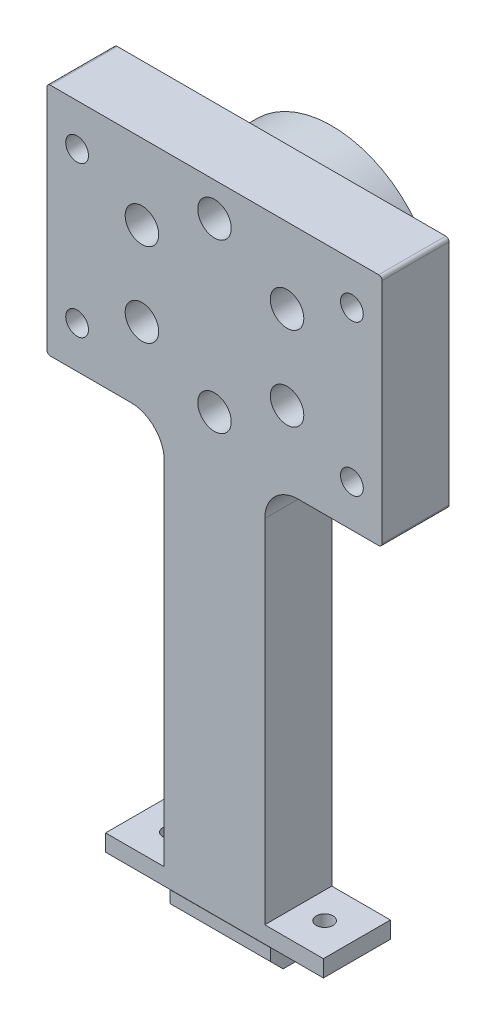
SolidWorks part; units mm, degrees
material "Lega 1060"
ref_plane "Piano frontale" through (0, 0, 0) normal (0, 0, 1) x (1, 0, 0)
ref_plane "Piano superiore" through (0, 0, 0) normal (0, 1, 0) x (1, 0, 0)
ref_plane "Piano destro" through (0, 0, 0) normal (1, 0, 0) x (0, 0, -1)
sketch "Schizzo1" plane through (0, 0, 0) normal (0, 0, 1) x (1, 0, 0)
  arc A6 (-1482, 0) -> (-1488, 0) centre (-1485, 0) ccw
  arc A7 (-1488, 0) -> (-1482, 0) centre (-1485, 0) ccw
  arc A8 (-1475.75, 0) -> (-1444.25, 0) centre (-1460, 0) ccw
  arc A9 (-1444.25, 0) -> (-1475.75, 0) centre (-1460, 0) ccw
extrude "Estrusione-Estrusione2" add sketch "Schizzo1" against normal blind 1
ref_point "Punto1"
sketch "Schizzo2" plane through (0, 0, 0) normal (0, 0, 1) x (1, 0, 0)
  arc A0 (-1479.1506, -12.5) -> (-1484.1506, -12.5) centre (-1481.6506, -12.5) ccw construction
  arc A1 (-1484.1506, -12.5) -> (-1479.1506, -12.5) centre (-1481.6506, -12.5) ccw construction
  arc A2 (-1457.5, -25) -> (-1462.5, -25) centre (-1460, -25) ccw construction
  arc A3 (-1462.5, -25) -> (-1457.5, -25) centre (-1460, -25) ccw construction
  arc A4 (-1435.8494, -12.5) -> (-1440.8494, -12.5) centre (-1438.3494, -12.5) ccw construction
  arc A5 (-1440.8494, -12.5) -> (-1435.8494, -12.5) centre (-1438.3494, -12.5) ccw construction
  arc A6 (-1435.8494, 12.5) -> (-1440.8494, 12.5) centre (-1438.3494, 12.5) ccw construction
  arc A7 (-1440.8494, 12.5) -> (-1435.8494, 12.5) centre (-1438.3494, 12.5) ccw construction
  arc A8 (-1462.5, 25) -> (-1457.5, 25) centre (-1460, 25) ccw construction
  arc A9 (-1457.5, 25) -> (-1462.5, 25) centre (-1460, 25) ccw construction
  arc A10 (-1479.1506, 12.5) -> (-1484.1506, 12.5) centre (-1481.6506, 12.5) ccw construction
  arc A11 (-1484.1506, 12.5) -> (-1479.1506, 12.5) centre (-1481.6506, 12.5) ccw construction
  arc A12 (-1479.1506, -12.5) -> (-1484.1506, -12.5) centre (-1481.6506, -12.5) ccw
  arc A13 (-1484.1506, -12.5) -> (-1479.1506, -12.5) centre (-1481.6506, -12.5) ccw
  arc A14 (-1457.5, -25) -> (-1462.5, -25) centre (-1460, -25) ccw
  arc A15 (-1462.5, -25) -> (-1457.5, -25) centre (-1460, -25) ccw
  arc A16 (-1435.8494, -12.5) -> (-1440.8494, -12.5) centre (-1438.3494, -12.5) ccw
  arc A17 (-1440.8494, -12.5) -> (-1435.8494, -12.5) centre (-1438.3494, -12.5) ccw
  arc A18 (-1435.8494, 12.5) -> (-1440.8494, 12.5) centre (-1438.3494, 12.5) ccw
  arc A19 (-1440.8494, 12.5) -> (-1435.8494, 12.5) centre (-1438.3494, 12.5) ccw
  arc A20 (-1462.5, 25) -> (-1457.5, 25) centre (-1460, 25) ccw
  arc A21 (-1457.5, 25) -> (-1462.5, 25) centre (-1460, 25) ccw
  arc A22 (-1479.1506, 12.5) -> (-1484.1506, 12.5) centre (-1481.6506, 12.5) ccw
  arc A23 (-1484.1506, 12.5) -> (-1479.1506, 12.5) centre (-1481.6506, 12.5) ccw
  arc A24 (-1491.5, 0) -> (-1428.5, 0) centre (-1460, 0) ccw construction
  arc A25 (-1428.5, 0) -> (-1491.5, 0) centre (-1460, 0) ccw construction
  arc A26 (-1491.5, 0) -> (-1428.5, 0) centre (-1460, 0) ccw
  arc A27 (-1428.5, 0) -> (-1491.5, 0) centre (-1460, 0) ccw
extrude "Estrusione-Estrusione3" add sketch "Schizzo2" along normal blind 15
sketch "Schizzo4" plane through (0, 0, 15) normal (0, 0, 1) x (1, 0, 0)
  line L0 (-1460, 0) -> (-1519.7962, 0) construction
  line L5 (-1510, 35) -> (-1410, 35)
  line L6 (-1510, 35) -> (-1510, -35)
  line L7 (-1510, -35) -> (-1410, -35)
  line L8 (-1410, 35) -> (-1410, -35)
  line L9 (-1460, 0) -> (-1460, 38.4815) construction
  circle A0 centre (-1501, 22.5) radius 3.4
  circle A2 centre (-1419, -22.5) radius 3.4
  circle A3 centre (-1419, 22.5) radius 3.4
  circle A16 centre (-1460, 0) radius 31.5 construction
  circle A17 centre (-1501, -22.5) radius 3.4
  dimension "D3" = 35
  dimension "D4" = 50
  dimension "D5" = 9
  dimension "D7" = 6.8
  dimension "D1" = 100
  dimension "D2" = 70
  dimension "D6" = 12.5
extrude "Estrusione-Estrusione4" add sketch "Schizzo4" along normal blind 20
sketch "Schizzo5" plane through (0, 0, -1) normal (0, 0, -1) x (-1, 0, 0)
  circle A0 centre (1438.3494, 12.5) radius 2.5
  circle A1 centre (1438.3494, -12.5) radius 2.5 construction
  circle A2 centre (1460, -25) radius 2.5 construction
  circle A3 centre (1481.6506, -12.5) radius 2.5 construction
  circle A4 centre (1481.6506, 12.5) radius 2.5 construction
  circle A5 centre (1460, 25) radius 2.5 construction
  circle A6 centre (1438.3494, -12.5) radius 2.5
  circle A7 centre (1460, -25) radius 2.5
  circle A8 centre (1481.6506, -12.5) radius 2.5
  circle A9 centre (1481.6506, 12.5) radius 2.5
  circle A10 centre (1460, 25) radius 2.5
extrude "Taglio-Estrusione2" cut sketch "Schizzo5" against normal up to surface (36 mm away) up to face at (-1422.4, -22.5, 35)
sketch "Schizzo6" plane through (0, 0, 35) normal (0, 0, 1) x (1, 0, 0)
  circle A1 centre (-1460, 25) radius 5
  circle A2 centre (-1438.3494, 12.5) radius 5
  circle A3 centre (-1438.3494, -12.5) radius 5
  circle A4 centre (-1460, -25) radius 5
  circle A5 centre (-1481.6506, -12.5) radius 5
  circle A29 centre (-1481.6506, 12.5) radius 5
  circle A30 centre (-1481.6506, 12.5) radius 5
  point P0 (-1460, 0)
  point P13 (-1460, 0)
  dimension "D1" = 2.5
  dimension "D2" = 6
extrude "Taglio-Estrusione3" cut sketch "Schizzo6" against normal blind 10
sketch "Schizzo7" plane through (0, 0, 15) normal (0, 0, -1) x (-1, 0, 0)
  circle A2 centre (1419, 22.5) radius 6
  circle A3 centre (1501, -22.5) radius 6
  circle A4 centre (1501, 22.5) radius 6
  circle A5 centre (1419, -22.5) radius 6
  dimension "D1" = 12
extrude "Taglio-Estrusione4" cut sketch "Schizzo7" against normal blind 8
fillet "Raccordo1" radius 1 4 edges at (-1510, -35, 25) (-1510, 35, 25) (-1410, -35, 25) (-1410, 35, 25)
fillet "Raccordo2" radius 1 1 edges at (-1428.5, 0, 15)
sketch "Schizzo8" plane through (0, 0, 35) normal (0, 0, 1) x (1, 0, 0)
  line L0 (-1509, -35) -> (-1411, -35) construction
  line L1 (-1460, -35) -> (-1475, -35)
  line L3 (-1465.76, -155) -> (-1475, -155)
  line L4 (-1475, -35) -> (-1475, -155)
  line L6 (-1460, -35) -> (-1445, -35)
  line L8 (-1465.76, -155) -> (-1445, -155)
  line L9 (-1445, -35) -> (-1445, -155)
  dimension "D1" = 15
  dimension "D2" = 15
extrude "Estrusione-Estrusione5" add sketch "Schizzo8" against normal up to surface (20 mm away) up to face at (-1427.5, 0, 15)
fillet "Raccordo3" radius 10 2 edges at (-1445, -35, 25) (-1475, -35, 25)
ref_plane "Piano1" through (0, 0, 25) normal (0, 0, -1) x (-1, 0, 0)
sketch "Schizzo10" plane through (-1475, 0, 0) normal (-1, 0, 0) x (0, 0, 1)
  line L0 (20.7, -155) -> (20.7, -156.76)
  line L1 (15, -155) -> (35, -155) construction
  line L2 (20.7, -156.76) -> (16.7, -156.76)
  line L3 (16.7, -156.76) -> (16.7, -160.36)
  line L7 (33.3, -160.36) -> (33.3, -156.76)
  line L8 (33.3, -156.76) -> (29.3, -156.76)
  line L9 (29.3, -156.76) -> (29.3, -155)
  line L10 (38, -155) -> (12, -155) construction
  line L11 (29.3, -155) -> (20.7, -155)
  line L12 (35, -45) -> (35, -155) construction
  line L13 (15, -155) -> (15, -45) construction
  line L14 (16.7, -160.36) -> (20.483, -164.143)
  line L15 (20.483, -164.143) -> (29.517, -164.143)
  line L16 (29.517, -164.143) -> (33.3, -160.36)
  dimension "D1" = 5.7
  dimension "D2" = 1.76
  dimension "D3" = 5.7
  dimension "D4" = 4
  dimension "D5" = 4
  dimension "D6" = 5.35
  dimension "D7" = 3.6
  dimension "D8" = 3.6
  dimension "D9" = 1.76
  dimension "D10" = 5.35
  dimension "D11" = 9.034
extrude "Estrusione-Estrusione6" add sketch "Schizzo10" against normal up to surface (30 mm away) up to face at (-1445, -100, 25)
sketch "Schizzo11" plane through (-1445, 0, 0) normal (1, 0, 0) x (0, 0, -1)
  line L0 (-15, -45) -> (-15, -155) construction
  line L1 (-35, -155) -> (-15, -155)
  line L2 (-35, -155) -> (-35, -150)
  line L3 (-35, -150) -> (-15, -150)
  line L4 (-15, -155) -> (-15, -150)
  dimension "D1" = 5
extrude "Estrusione-Estrusione7" add sketch "Schizzo11" along normal blind 17.5 and the other way blind 47.5
sketch "Schizzo13" plane through (0, -155, 0) normal (0, -1, 0) x (1, 0, 0)
  circle A0 centre (-1437.15, 25) radius 2.5 construction
  circle A1 centre (-1482.85, 25) radius 2.5 construction
  circle A2 centre (-1437.15, 25) radius 2.5
  circle A3 centre (-1482.85, 25) radius 2.5
extrude "Taglio-Estrusione5" cut sketch "Schizzo13" against normal up to next
